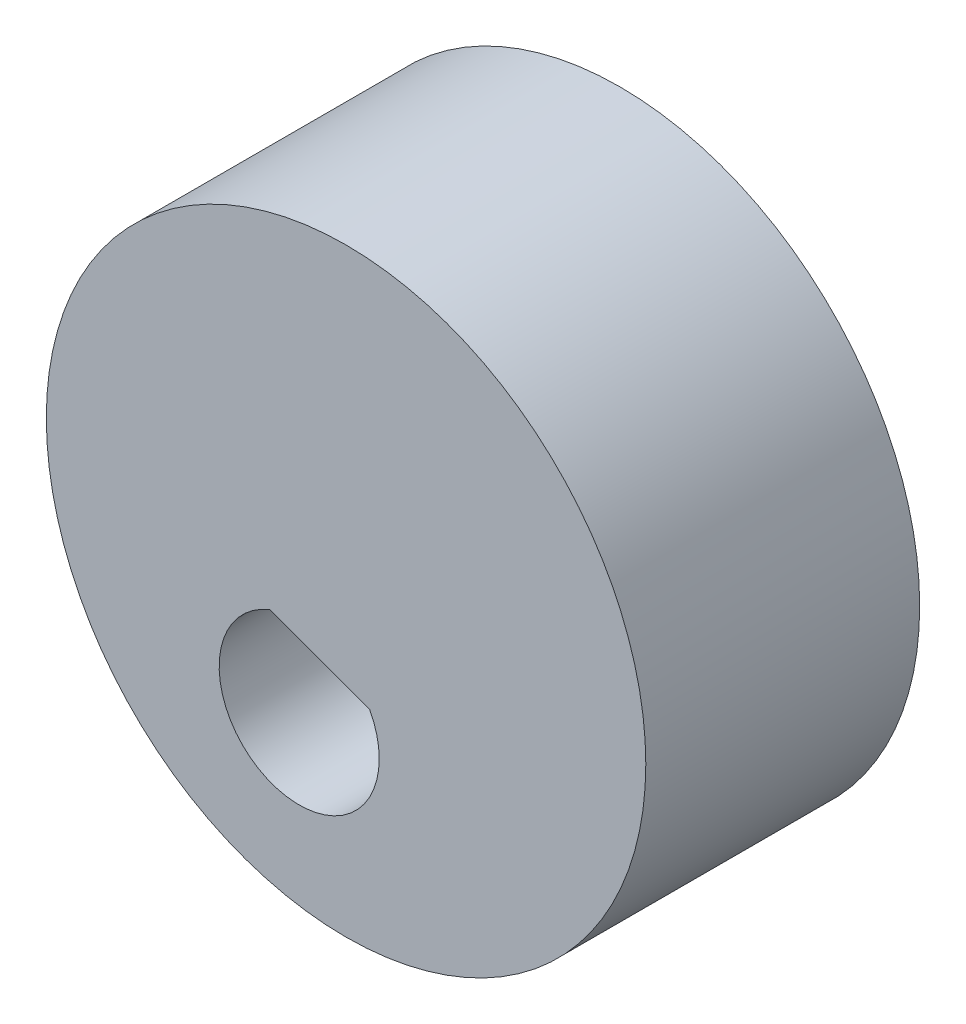
SolidWorks part; units mm, degrees
ref_plane "Front Plane" through (0, 0, 0) normal (0, 0, 1) x (1, 0, 0)
ref_plane "Top Plane" through (0, 0, 0) normal (0, 1, 0) x (1, 0, 0)
ref_plane "Right Plane" through (0, 0, 0) normal (1, 0, 0) x (0, 0, -1)
sketch "Sketch2" plane through (0, 0, -65.7668) normal (0, 0, 1) x (1, 0, 0)
  line L0 (-20.1422, -37.1244) -> (-18.6022, -32.8961) construction
  line L1 (-18.6022, -32.8961) -> (-27.8575, -29.5253) construction
  line L2 (-17.8257, -35.8791) -> (-21.0952, -34.6732) construction
  line L3 (-21.0952, -34.6732) -> (-17.8257, -35.8791)
  circle A0 centre (-18.6022, -32.8961) radius 9.85
  arc A1 (-21.0952, -34.6732) -> (-17.8257, -35.8791) centre (-20.1422, -37.1244) ccw construction
  arc A2 (-17.8257, -35.8791) -> (-21.0952, -34.6732) centre (-20.1422, -37.1244) cw
  dimension "D1" = 4.5
extrude "Boss-Extrude1" add sketch "Sketch2" along normal up to surface (9 mm away)
